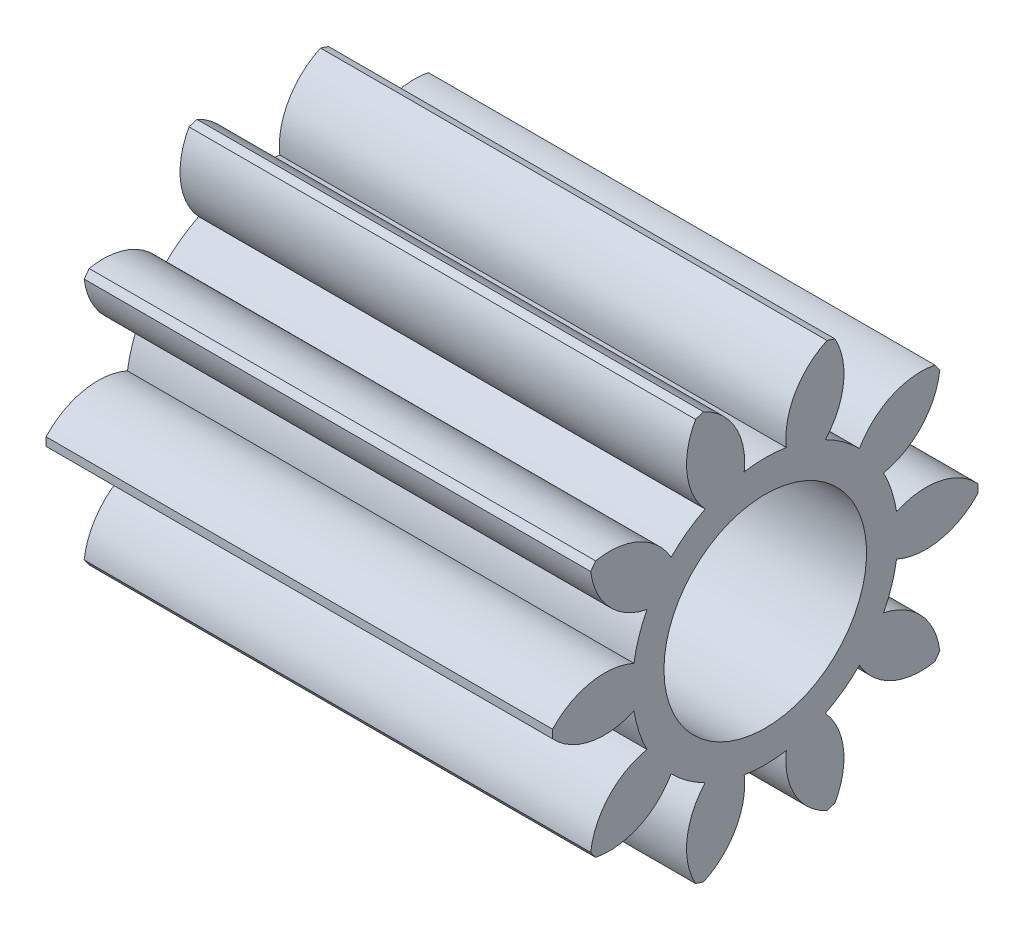
SolidWorks part; units mm, degrees
ref_plane "Plane1" through (0, 0, 0) normal (0, 0, 1) x (1, 0, 0)
ref_plane "Plane2" through (0, 0, 0) normal (0, 1, 0) x (1, 0, 0)
ref_plane "Plane3" through (0, 0, 0) normal (1, 0, 0) x (0, 0, -1)
sketch "HoldingSke" plane through (0, 0, 0) normal (0, 1, 0) x (1, 0, 0)
  line L0 (0, 0) -> (1.4069, -0.2481)
  line L1 (-15, 0) -> (100, 0) construction
  line L2 (0, 0) -> (-2.1039, 2.3779)
  line L3 (0, 0) -> (-11.863, 4.5341)
  line L4 (0, 0) -> (8.5048, 1.4996)
  line L5 (0, 0) -> (-46.8476, -17.4728)
  line L6 (0, 0) -> (-8.2896, -5.593)
  line L7 (-2.1039, 2.3779) -> (8.6586, 51.2059)
  line L8 (-76.2, 54.61) -> (-75.5, 54.61)
  line L9 (-71.009, 38.7566) -> (-53.1078, 45.2721)
  line L10 (-76.2, 71.12) -> (104.1128, 71.12)
  line L11 (0, 0) -> (-10, 0)
  line L12 (-76.2, 101.6) -> (-76.173, 101.6)
  line L13 (24.9733, 27.94) -> (52.9518, 28.4284)
  line L14 (24.9733, 27.94) -> (24.9743, 27.94)
  line L15 (24.9733, 27.94) -> (100.4006, 29.5858)
  line L16 (-63.627, -0.7) -> (-12.827, -0.7)
  circle A0 centre (0, 0) radius 2
  circle A1 centre (0, 0) radius 2.624
  circle A2 centre (0, 0) radius 37.5
  circle A3 centre (0, 0) radius 2
  dimension "MHD" = 5.248
  dimension "Hub_dia" = 75
  dimension "Bore" = 4
  dimension "MBD" = 4
  dimension "Num_teeth" = 10
  dimension "Pitch_radius" = 180.3128
  dimension "Pitch" = 1.4286
  dimension "Width" = 10
  dimension "Overall_len" = 50
  dimension "Show_teeth" = 10
  dimension "Thickness" = 10
  dimension "OAL" = 50.0001
  dimension "T_dim" = 0.7
  dimension "Ap" = 20
  dimension "H" = 19.05
  dimension "Backlash" = 0.027
  dimension "Addendum_fac" = 1
  dimension "Dedendum_fac" = 1.25
  dimension "Clearance_fac" = 0.25
  dimension "Dedendum_add" = 0.001
  dimension "Module" = 0.7
sketch "BasProSke" plane through (0, 0, 0) normal (0, 1, 0) x (1, 0, 0)
  line L0 (-10, 0) -> (60, 0) construction
  line L1 (0, 0) -> (0, 4.2)
  line L2 (0, 0) -> (10, 0)
  line L3 (10, 0) -> (10, 4.2)
  line L4 (10, 4.2) -> (0, 4.2)
  dimension "Diameter" = 8.4
  dimension "Thickness" = 10
revolve "Base-Revolve" add sketch "BasProSke" angle 360 about L0
sketch "TooCutSke" plane through (0, 0, 0) normal (1, 0, 0) x (0, 0, -1)
  line L1 (0, 0) -> (0, 107) construction
  line L2 (0, 0) -> (-0.5947, 3.4491) construction
  line L3 (0, 0) -> (-2.1409, 6.589) construction
  line L4 (-0.5947, 3.4491) -> (-1.0705, 3.2945) construction
  arc A0 (0.4155, 2.5909) -> (-0.4155, 2.5909) centre (0, 0) ccw
  arc A1 (1.2546, 4.0349) -> (-1.2546, 4.0349) centre (0, 0) ccw
  circle A2 centre (0, 0) radius 3.5 construction
  circle A3 centre (0, 0) radius 3.2889 construction
  arc A4 (-0.4155, 2.5909) -> (-1.2546, 4.0349) centre (-1.8066, 2.7483) ccw
  arc A5 (1.2546, 4.0349) -> (0.4155, 2.5909) centre (1.8066, 2.7483) ccw
  dimension "Root_dia" = 5.248
  dimension "Overcut_dia" = 8.4508
  dimension "Pitch_dia" = 7
  dimension "Base_dia" = 6.5778
  dimension "Flank_rad" = 1.4
  dimension "Half_ang" = 18
  dimension "Half_CT" = 0.5003
extrude "ToothCut" cut sketch "TooCutSke" along normal through all
fillet "Breaks" [suppressed] radius 0.014
fillet "RootFillets" [suppressed] radius 0.176
pattern_circular "TeethCuts" count 10 every 36 about axis through (-10, 0, 0) along (1, 0, 0) of "ToothCut", "RootFillets", "Breaks"
sketch "HubNeaOneSke" plane through (0, 0, 0) normal (-1, 0, 0) x (0, 0, 1)
  circle A0 centre (0, 0) radius 2.624
  dimension "Diameter" = 5.248
extrude "HubNearOne" [suppressed] add sketch "HubNeaOneSke" along normal blind 40.0001
sketch "HubNeaBotSke" plane through (0, 0, 0) normal (-1, 0, 0) x (0, 0, 1)
  circle A0 centre (0, 0) radius 2.624
  dimension "Diameter" = 5.248
extrude "HubNearBoth" [suppressed] add sketch "HubNeaBotSke" along normal blind 20
ref_plane "FarPln" through (10, 0, 0) normal (1, 0, 0) x (0, 0, -1)
sketch "HubFarSke" plane through (10, 0, 0) normal (1, 0, 0) x (0, 0, -1)
  circle A0 centre (0, 0) radius 2.624
  dimension "Diameter" = 5.248
extrude "HubFar" [suppressed] add sketch "HubFarSke" along normal blind 20
sketch "BorSke" plane through (0, 0, 0) normal (1, 0, 0) x (0, 0, -1)
  circle A0 centre (0, 0) radius 2
  dimension "Diameter" = 4
extrude "Bore" cut sketch "BorSke" along normal mid plane 100.0001
sketch "KeySke" plane through (0, 0, 0) normal (1, 0, 0) x (0, 0, -1)
  line L0 (-0.8, 0) -> (-0.8, 2.7)
  line L1 (-0.8, 2.7) -> (0.8, 2.7)
  line L2 (0.8, 2.7) -> (0.8, 0)
  line L3 (0, 0) -> (0, 34) construction
  line L4 (-0.8, 0) -> (0.8, 0)
  dimension "Offset" = 2.7
  dimension "Width" = 1.6
extrude "Keyway" [suppressed] cut sketch "KeySke" along normal mid plane 100.0001
pattern_circular "Keyway2" [suppressed] count 2 every 90 about axis through (-10, 0, 0) along (1, 0, 0)
equation "' \"Module@HoldingSke\" = 6.35"
equation "' \"Num_teeth@HoldingSke\" = 12"
equation "' \"Ap@HoldingSke\" =  20"
equation "' \"Width@HoldingSke\" = 0.5 * 25.4"
equation "' \"Hub_dia@HoldingSke\"= 1 * 25.4"
equation "' \"Overall_len@HoldingSke\" = 1.0 * 25.4"
equation "' \"Bore@HoldingSke\" = 0.75 * 25.4"
equation "' \"T_dim@HoldingSke\" = 0.1 * 25.4"
equation "' \"Width@KeySke\" = 0.25 * 25.4"
equation "' \"Show_teeth@HoldingSke\" = 13"
equation "' \"Backlash@HoldingSke\" = 0.009 * 25.4"
equation "' \"Addendum_fac@HoldingSke\" = 1.0"
equation "' \"Dedendum_fac@HoldingSke\" = 1.25"
equation "' \"Dedendum_add@HoldingSke\" = 0.00005 * 25.4"
equation "' \"Clearance_fac@HoldingSke\" = 0.25"
equation "\"Pitch@HoldingSke\" = 1 / \"Module@HoldingSke\""
equation "\"Overcut_dia@TooCutSke\" = (\"Num_teeth@HoldingSke\" + 2 * \"Addendum_fac@HoldingSke\") / \"Pitch@HoldingSke\" + 0.002 * 25.4"
equation "\"Pitch_dia@TooCutSke\" = \"Num_teeth@HoldingSke\" / \"Pitch@HoldingSke\""
equation "\"Base_dia@TooCutSke\" = \"Num_teeth@HoldingSke\" / \"Pitch@HoldingSke\" * cos((\"Ap@HoldingSke\"  * 3.14159265 / 180))"
equation "\"Root_dia@TooCutSke\" = (\"Num_teeth@HoldingSke\" + 2) / \"Pitch@HoldingSke\" - 2 * (\"Addendum_fac@HoldingSke\" + \"Dedendum_fac@HoldingSke\") / \"Pitch@HoldingSke\" - \"Dedendum_add@HoldingSke\" * 2"
equation "\"Half_ang@TooCutSke\" = 180 / \"Num_teeth@HoldingSke\""
equation "\"Half_CT@TooCutSke\" = \"Num_teeth@HoldingSke\" / \"Pitch@HoldingSke\" * sin((3.14159265 / 2 / \"Num_teeth@HoldingSke\")) / 2 - 7 * \"Backlash@HoldingSke\" / 4"
equation "\"Flank_rad@TooCutSke\" = \"Num_teeth@HoldingSke\" / \"Pitch@HoldingSke\" / 5"
equation "\"Radius@RootFillets\" = \"Clearance_fac@HoldingSke\" / \"Pitch@HoldingSke\" + \"Dedendum_add@HoldingSke\""
equation "\"Break_rad@Breaks\" = 0.02 / \"Pitch@HoldingSke\""
equation "\"Thickness@HoldingSke\" = \"Width@HoldingSke\""
equation "\"OAL@HoldingSke\" = \"Thickness@HoldingSke\""
equation "\"MHD@HoldingSke\" = (\"Num_teeth@HoldingSke\" + 2) / \"Pitch@HoldingSke\" - 2 * (\"Addendum_fac@HoldingSke\" + \"Dedendum_fac@HoldingSke\")  / \"Pitch@HoldingSke\" - \"Dedendum_add@HoldingSke\" * 2"
equation "\"MBD@HoldingSke\" = (\"Num_teeth@HoldingSke\" + 2) / \"Pitch@HoldingSke\" - 2 * (\"Addendum_fac@HoldingSke\" + \"Dedendum_fac@HoldingSke\")  / \"Pitch@HoldingSke\" - \"Dedendum_add@HoldingSke\" * 2 - 0.002 * 25.4"
equation "\"MHD@HoldingSke\" = ((sgn( \"MHD@HoldingSke\" - \"Hub_dia@HoldingSke\" )-1)*( \"MHD@HoldingSke\" - \"Hub_dia@HoldingSke\" ))/-2+ \"Hub_dia@HoldingSke\""
equation "\"MBD@HoldingSke\" = ((sgn( \"MBD@HoldingSke\" - \"Bore@HoldingSke\" )-1)*( \"MBD@HoldingSke\" - \"Bore@HoldingSke\" ))/-2+ \"Bore@HoldingSke\""
equation "\"OAL@HoldingSke\" = ((sgn( \"OAL@HoldingSke\" - \"Overall_len@HoldingSke\" )+1)*( \"OAL@HoldingSke\" - \"Overall_len@HoldingSke\" ))/2 + \"Overall_len@HoldingSke\" + 0.000002 * 25.4"
equation "\"Num_teeth@TeethCuts\" = int( \"Show_teeth@HoldingSke\" ) + 1"
equation "\"Num_teeth@TeethCuts\" = ((sgn( \"Num_teeth@TeethCuts\" - \"Num_teeth@HoldingSke\" )-1)*( \"Num_teeth@TeethCuts\" - \"Num_teeth@HoldingSke\" ))/-2+ \"Num_teeth@HoldingSke\""
equation "\"Num_teeth@TeethCuts\" = ((sgn( \"Num_teeth@TeethCuts\" - 2.0)+1)*( \"Num_teeth@TeethCuts\" - 2.0))/2 +2.0"
equation "\"Angle@TeethCuts\" = 360.0 / \"Num_teeth@HoldingSke\""
equation "\"Diameter@BasProSke\" = (\"Num_teeth@HoldingSke\" + 2 * \"Addendum_fac@HoldingSke\") / \"Pitch@HoldingSke\""
equation "\"Thickness@BasProSke\"  = \"Thickness@HoldingSke\""
equation "' \"Fillet_rad@BasProSke\" =  \"Thickness@HoldingSke\" * 0.05"
equation "\"MHD@HoldingSke\" = ((sgn( \"MHD@HoldingSke\" - \"Root_dia@TooCutSke\" )-1)*( \"MHD@HoldingSke\" - \"Root_dia@TooCutSke\" ))/-2+ \"Root_dia@TooCutSke\""
equation "\"Diameter@HubNeaOneSke\" = \"MHD@HoldingSke\""
equation "\"Length@HubNearOne\" = \"OAL@HoldingSke\" - \"Thickness@BasProSke\""
equation "\"Diameter@HubNeaBotSke\" = \"MHD@HoldingSke\""
equation "\"Length@HubNearBoth\" = ( \"OAL@HoldingSke\" - \"Thickness@BasProSke\" ) / 2.0"
equation "\"Thickness@FarPln\" = \"Thickness@BasProSke\""
equation "\"Diameter@HubFarSke\" = \"MHD@HoldingSke\""
equation "\"Length@HubFar\" = ( \"OAL@HoldingSke\" - \"Thickness@BasProSke\" ) / 2.0"
equation "\"Diameter@BorSke\" = \"MBD@HoldingSke\""
equation "\"D1@Bore\" = \"OAL@HoldingSke\" * 2.0"
equation "\"D1@Keyway\" = \"OAL@HoldingSke\" * 2.0"
equation "\"Offset@KeySke\" = \"T_dim@HoldingSke\" + \"MBD@HoldingSke\" / 2.0"
